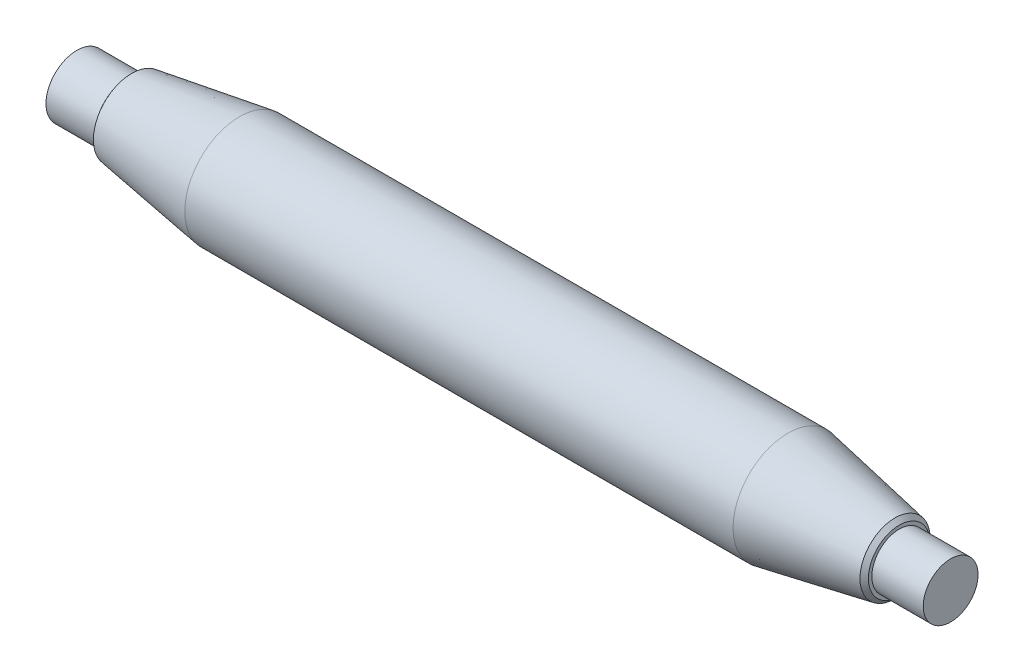
SolidWorks part; units mm, degrees
ref_plane "Plan de face" through (0, 0, 0) normal (0, 0, 1) x (1, 0, 0)
ref_plane "Plan de dessus" through (0, 0, 0) normal (0, 1, 0) x (1, 0, 0)
ref_plane "Plan de droite" through (0, 0, 0) normal (1, 0, 0) x (0, 0, -1)
sketch "Esquisse1" plane through (0, 0, 0) normal (0, 0, 1) x (1, 0, 0)
  line L0 (-74.93, 0) -> (189.2868, 0) construction
  line L1 (-127.5, 0) -> (-127.5, 9)
  line L2 (-127.5, 9) -> (-112.5, 9)
  line L3 (-112.5, 9) -> (-112.5, 11)
  line L4 (-112.5, 11) -> (-80, 16)
  line L5 (-80, 16) -> (80, 16)
  line L6 (-127.5, 0) -> (127.5, 0)
  line L7 (0, 0) -> (0, 16) construction
  line L8 (112.5, 10) -> (80, 16)
  line L9 (112.5, 8) -> (112.5, 10)
  line L10 (127.5, 8) -> (112.5, 8)
  line L11 (127.5, 0) -> (127.5, 8)
  point P15 (106.8069, 9)
  dimension "D1" = 18
  dimension "D2" = 32
  dimension "D3" = 15
  dimension "D4" = 255
  dimension "D5" = 80
  dimension "D6" = 22
  dimension "D7" = 16
  dimension "D8" = 2
revolve "Révolution1" add sketch "Esquisse1" angle 360 about L6
chamfer "Chanfrein1" distance 1 angle 45 2 edges at (-112.5, 0, 11) (112.5, 0, 10)
sketch "Esquisse2" plane through (0, 0, 0) normal (0, 1, 0) x (1, 0, 0)
  line L0 (-25, 16) -> (-24.3221, 11.1763)
  line L1 (-24.3221, 11.1763) -> (10, 16)
  line L2 (10, 16) -> (-25, 16)
  line L3 (80, 16) -> (-80, 16) construction
  line L5 (-7.5, 16) -> (-7.5, 56.1619) construction
  line L6 (-112.5, 9) -> (-112.5, -9) construction
  dimension "D1" = 8
  dimension "D2" = 105
  dimension "D3" = 35
extrude "Enlèv. mat.-Extru.1" cut sketch "Esquisse2" against normal through all both and the other way through all
